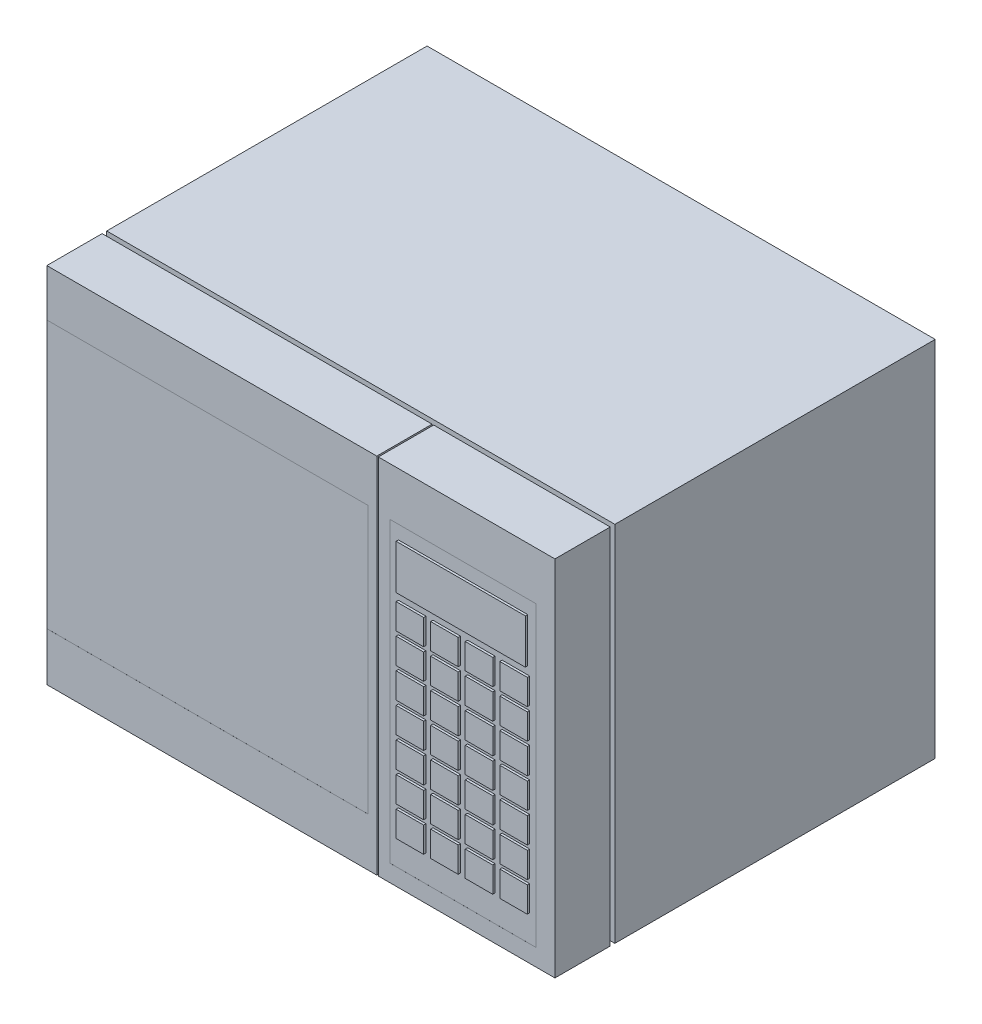
SolidWorks part; units mm, degrees
ref_plane "Front Plane" through (0, 0, 0) normal (0, 0, 1) x (1, 0, 0)
ref_plane "Top Plane" through (0, 0, 0) normal (0, 1, 0) x (1, 0, 0)
ref_plane "Right Plane" through (0, 0, 0) normal (1, 0, 0) x (0, 0, -1)
sketch "Sketch1" plane through (0, 0, 0) normal (0, 0, 1) x (1, 0, 0)
  line L1 (-118.8061, 195.1275) -> (441.1939, 195.1275)
  line L2 (-118.8061, 195.1275) -> (-118.8061, -204.8725)
  line L3 (-118.8061, -204.8725) -> (441.1939, -204.8725)
  line L4 (441.1939, 195.1275) -> (441.1939, -204.8725)
  dimension "D1" = 560
  dimension "D2" = 400
extrude "Boss-Extrude1" add sketch "Sketch1" along normal blind 419.1
sketch "Sketch2" plane through (0, 0, 419.1) normal (0, 0, 1) x (1, 0, 0)
  line L1 (-274.6839, 143.2103) -> (235.0784, 143.2103)
  line L2 (-274.6839, 143.2103) -> (-274.6839, -151.3981)
  line L3 (-274.6839, -151.3981) -> (235.0784, -151.3981)
  line L4 (235.0784, 143.2103) -> (235.0784, -151.3981)
  line L5 (259.4465, 141.957) -> (420.0766, 141.957)
  line L6 (259.4465, 141.957) -> (259.4465, -186.1594)
  line L7 (259.4465, -186.1594) -> (420.0766, -186.1594)
  line L8 (420.0766, 141.957) -> (420.0766, -186.1594)
extrude "Cut-Extrude1" cut sketch "Sketch2" against normal blind 0.0254
sketch "Sketch3" plane through (0, 0, 419.1) normal (0, 0, 1) x (1, 0, 0)
  line L0 (441.1939, 195.1275) -> (-118.8061, 195.1275) construction
  line L1 (-317.7581, 195.1275) -> (441.1939, 195.1275)
  line L2 (-317.7581, 195.1275) -> (-317.7581, -204.8725)
  line L3 (-317.7581, -204.8725) -> (441.1939, -204.8725)
  line L4 (441.1939, 195.1275) -> (441.1939, -204.8725)
  line L6 (-311.5739, 176.2378) -> (433.789, 176.2378)
  line L7 (-311.5739, 176.2378) -> (-311.5739, -196.9334)
  line L8 (-311.5739, -196.9334) -> (433.789, -196.9334)
  line L9 (433.789, 176.2378) -> (433.789, -196.9334)
extrude "Cut-Extrude2" cut sketch "Sketch3" against normal blind 5.08 from offset 60.96 offset against normal yes
sketch "Sketch5" plane through (0, 0, 419.0746) normal (0, 0, 1) x (1, 0, 0)
  line L0 (306.7543, 69.4007) -> (337.0946, 69.4007)
  line L1 (268.6543, 126.9695) -> (411.0202, 126.9695)
  line L2 (268.6543, 126.9695) -> (268.6543, 77.9583)
  line L3 (268.6543, 77.9583) -> (411.0202, 77.9583)
  line L4 (411.0202, 126.9695) -> (411.0202, 77.9583)
  line L5 (268.6543, 69.4007) -> (298.9946, 69.4007)
  line L6 (268.6543, 69.4007) -> (268.6543, 41.3943)
  line L7 (268.6543, 41.3943) -> (298.9946, 41.3943)
  line L8 (298.9946, 69.4007) -> (298.9946, 41.3943)
  line L9 (306.7543, 69.4007) -> (306.7543, 41.3943)
  line L10 (306.7543, 41.3943) -> (337.0946, 41.3943)
  line L11 (337.0946, 69.4007) -> (337.0946, 41.3943)
  line L12 (344.8543, 69.4007) -> (375.1946, 69.4007)
  line L13 (344.8543, 69.4007) -> (344.8543, 41.3943)
  line L14 (344.8543, 41.3943) -> (375.1946, 41.3943)
  line L15 (375.1946, 69.4007) -> (375.1946, 41.3943)
  line L16 (382.9543, 69.4007) -> (413.2946, 69.4007)
  line L17 (382.9543, 69.4007) -> (382.9543, 41.3943)
  line L18 (382.9543, 41.3943) -> (413.2946, 41.3943)
  line L19 (413.2946, 69.4007) -> (413.2946, 41.3943)
  line L20 (306.7543, 36.3807) -> (337.0946, 36.3807)
  line L21 (306.7543, 36.3807) -> (306.7543, 8.3743)
  line L22 (306.7543, 8.3743) -> (337.0946, 8.3743)
  line L23 (337.0946, 36.3807) -> (337.0946, 8.3743)
  line L24 (344.8543, 36.3807) -> (375.1946, 36.3807)
  line L25 (344.8543, 36.3807) -> (344.8543, 8.3743)
  line L26 (344.8543, 8.3743) -> (375.1946, 8.3743)
  line L27 (375.1946, 36.3807) -> (375.1946, 8.3743)
  line L28 (382.9543, 36.3807) -> (413.2946, 36.3807)
  line L29 (382.9543, 36.3807) -> (382.9543, 8.3743)
  line L30 (382.9543, 8.3743) -> (413.2946, 8.3743)
  line L31 (413.2946, 36.3807) -> (413.2946, 8.3743)
  line L32 (306.7543, 3.3607) -> (337.0946, 3.3607)
  line L33 (306.7543, 3.3607) -> (306.7543, -24.6457)
  line L34 (306.7543, -24.6457) -> (337.0946, -24.6457)
  line L35 (337.0946, 3.3607) -> (337.0946, -24.6457)
  line L36 (344.8543, 3.3607) -> (375.1946, 3.3607)
  line L37 (344.8543, 3.3607) -> (344.8543, -24.6457)
  line L38 (344.8543, -24.6457) -> (375.1946, -24.6457)
  line L39 (375.1946, 3.3607) -> (375.1946, -24.6457)
  line L40 (382.9543, 3.3607) -> (413.2946, 3.3607)
  line L41 (382.9543, 3.3607) -> (382.9543, -24.6457)
  line L42 (382.9543, -24.6457) -> (413.2946, -24.6457)
  line L43 (413.2946, 3.3607) -> (413.2946, -24.6457)
  line L44 (306.7543, -29.6593) -> (337.0946, -29.6593)
  line L45 (306.7543, -29.6593) -> (306.7543, -57.6657)
  line L46 (306.7543, -57.6657) -> (337.0946, -57.6657)
  line L47 (337.0946, -29.6593) -> (337.0946, -57.6657)
  line L48 (344.8543, -29.6593) -> (375.1946, -29.6593)
  line L49 (344.8543, -29.6593) -> (344.8543, -57.6657)
  line L50 (344.8543, -57.6657) -> (375.1946, -57.6657)
  line L51 (375.1946, -29.6593) -> (375.1946, -57.6657)
  line L52 (382.9543, -29.6593) -> (413.2946, -29.6593)
  line L53 (382.9543, -29.6593) -> (382.9543, -57.6657)
  line L54 (382.9543, -57.6657) -> (413.2946, -57.6657)
  line L55 (413.2946, -29.6593) -> (413.2946, -57.6657)
  line L56 (306.7543, -62.6793) -> (337.0946, -62.6793)
  line L57 (306.7543, -62.6793) -> (306.7543, -90.6857)
  line L58 (306.7543, -90.6857) -> (337.0946, -90.6857)
  line L59 (337.0946, -62.6793) -> (337.0946, -90.6857)
  line L60 (344.8543, -62.6793) -> (375.1946, -62.6793)
  line L61 (344.8543, -62.6793) -> (344.8543, -90.6857)
  line L62 (344.8543, -90.6857) -> (375.1946, -90.6857)
  line L63 (375.1946, -62.6793) -> (375.1946, -90.6857)
  line L64 (382.9543, -62.6793) -> (413.2946, -62.6793)
  line L65 (382.9543, -62.6793) -> (382.9543, -90.6857)
  line L66 (382.9543, -90.6857) -> (413.2946, -90.6857)
  line L67 (413.2946, -62.6793) -> (413.2946, -90.6857)
  line L68 (306.7543, -95.6993) -> (337.0946, -95.6993)
  line L69 (306.7543, -95.6993) -> (306.7543, -123.7057)
  line L70 (306.7543, -123.7057) -> (337.0946, -123.7057)
  line L71 (337.0946, -95.6993) -> (337.0946, -123.7057)
  line L72 (344.8543, -95.6993) -> (375.1946, -95.6993)
  line L73 (344.8543, -95.6993) -> (344.8543, -123.7057)
  line L74 (344.8543, -123.7057) -> (375.1946, -123.7057)
  line L75 (375.1946, -95.6993) -> (375.1946, -123.7057)
  line L76 (382.9543, -95.6993) -> (413.2946, -95.6993)
  line L77 (382.9543, -95.6993) -> (382.9543, -123.7057)
  line L78 (382.9543, -123.7057) -> (413.2946, -123.7057)
  line L79 (413.2946, -95.6993) -> (413.2946, -123.7057)
  line L80 (306.7543, -128.7193) -> (337.0946, -128.7193)
  line L81 (306.7543, -128.7193) -> (306.7543, -156.7257)
  line L82 (306.7543, -156.7257) -> (337.0946, -156.7257)
  line L83 (337.0946, -128.7193) -> (337.0946, -156.7257)
  line L84 (344.8543, -128.7193) -> (375.1946, -128.7193)
  line L85 (344.8543, -128.7193) -> (344.8543, -156.7257)
  line L86 (344.8543, -156.7257) -> (375.1946, -156.7257)
  line L87 (375.1946, -128.7193) -> (375.1946, -156.7257)
  line L88 (382.9543, -128.7193) -> (413.2946, -128.7193)
  line L89 (382.9543, -128.7193) -> (382.9543, -156.7257)
  line L90 (382.9543, -156.7257) -> (413.2946, -156.7257)
  line L91 (413.2946, -128.7193) -> (413.2946, -156.7257)
  line L92 (268.6543, 36.3807) -> (298.9946, 36.3807)
  line L93 (268.6543, 36.3807) -> (268.6543, 8.3743)
  line L94 (268.6543, 8.3743) -> (298.9946, 8.3743)
  line L95 (298.9946, 36.3807) -> (298.9946, 8.3743)
  line L96 (268.6543, 3.3607) -> (298.9946, 3.3607)
  line L97 (268.6543, 3.3607) -> (268.6543, -24.6457)
  line L98 (268.6543, -24.6457) -> (298.9946, -24.6457)
  line L99 (298.9946, 3.3607) -> (298.9946, -24.6457)
  line L100 (268.6543, -29.6593) -> (298.9946, -29.6593)
  line L101 (268.6543, -29.6593) -> (268.6543, -57.6657)
  line L102 (268.6543, -57.6657) -> (298.9946, -57.6657)
  line L103 (298.9946, -29.6593) -> (298.9946, -57.6657)
  line L104 (268.6543, -62.6793) -> (298.9946, -62.6793)
  line L105 (268.6543, -62.6793) -> (268.6543, -90.6857)
  line L106 (268.6543, -90.6857) -> (298.9946, -90.6857)
  line L107 (298.9946, -62.6793) -> (298.9946, -90.6857)
  line L108 (268.6543, -95.6993) -> (298.9946, -95.6993)
  line L109 (268.6543, -95.6993) -> (268.6543, -123.7057)
  line L110 (268.6543, -123.7057) -> (298.9946, -123.7057)
  line L111 (298.9946, -95.6993) -> (298.9946, -123.7057)
  line L112 (268.6543, -128.7193) -> (298.9946, -128.7193)
  line L113 (268.6543, -128.7193) -> (268.6543, -156.7257)
  line L114 (268.6543, -156.7257) -> (298.9946, -156.7257)
  line L115 (298.9946, -128.7193) -> (298.9946, -156.7257)
  dimension "D1" = 4
  dimension "D2" = 7
extrude "Boss-Extrude3" add sketch "Sketch5" along normal blind 2.54
sketch "Sketch6" plane through (0, 0, 419.1) normal (0, 0, 1) x (1, 0, 0)
  line L0 (441.1939, 195.1275) -> (-118.8061, 195.1275) construction
  line L1 (244.8696, 195.1275) -> (246.5894, 195.1275)
  line L2 (244.8696, 195.1275) -> (244.8696, -204.8725)
  line L3 (244.8696, -204.8725) -> (246.5894, -204.8725)
  line L4 (246.5894, 195.1275) -> (246.5894, -204.8725)
  line L5 (-118.8061, -204.8725) -> (441.1939, -204.8725) construction
extrude "Cut-Extrude3" cut sketch "Sketch6" against normal blind 63.5
